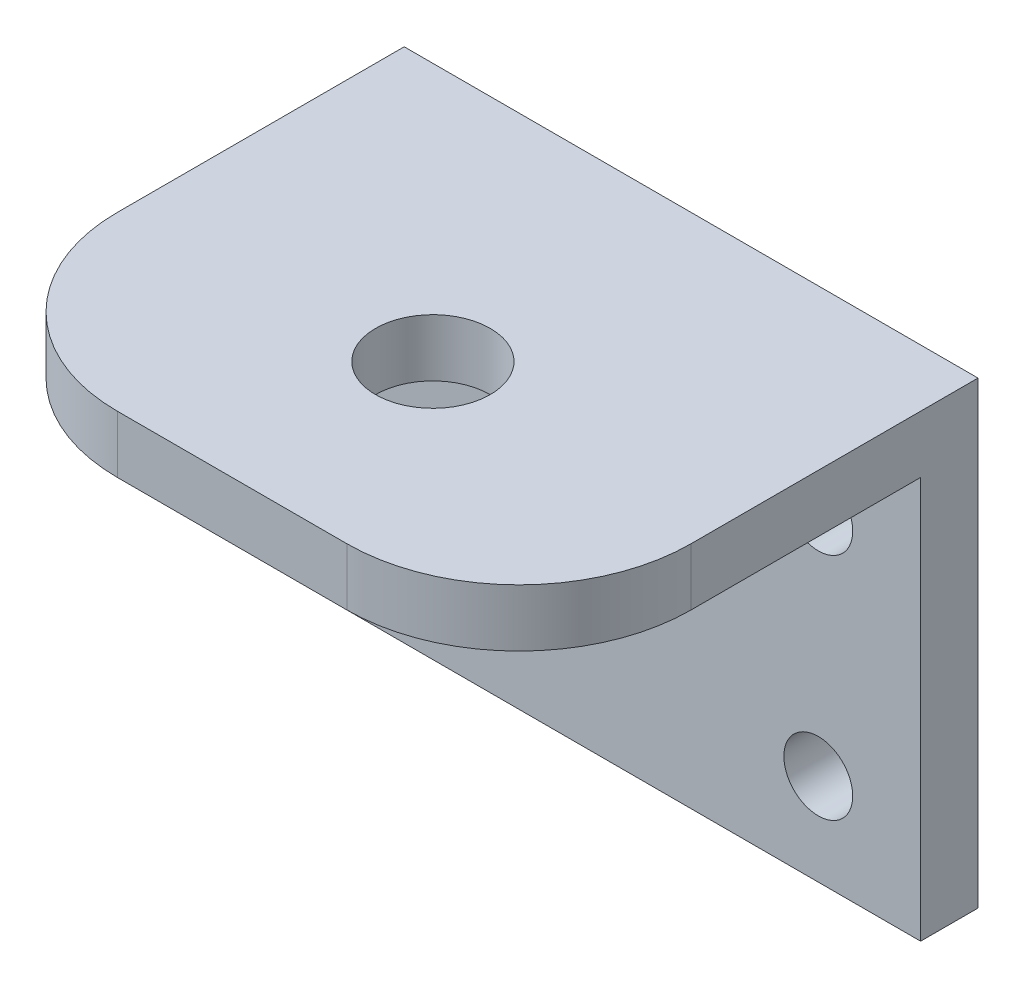
SolidWorks part; units mm, degrees
ref_plane "Front Plane" through (0, 0, 0) normal (0, 0, 1) x (1, 0, 0)
ref_plane "Top Plane" through (0, 0, 0) normal (0, 1, 0) x (1, 0, 0)
ref_plane "Right Plane" through (0, 0, 0) normal (1, 0, 0) x (0, 0, -1)
sketch "Sketch1" plane through (0, 0, 0) normal (0, 0, 1) x (1, 0, 0)
  line L1 (-25, -20) -> (25, -20)
  line L2 (-25, -20) -> (-25, 20)
  line L3 (-25, 20) -> (25, 20)
  line L4 (25, -20) -> (25, 20)
  line L5 (-25, -20) -> (25, 20) construction
  line L6 (-25, 20) -> (25, -20) construction
  point P0 (0, 0)
  dimension "D1" = 50
  dimension "D2" = 40
extrude "Boss-Extrude1" add sketch "Sketch1" along normal blind 40
sketch "Sketch2" plane through (0, 0, 0) normal (0, 0, -1) x (-1, 0, 0)
  line L1 (-16.0828, -12) -> (13.9172, -12) construction
  line L2 (-16.0828, -12) -> (-16.0828, 8) construction
  line L3 (-16.0828, 8) -> (13.9172, 8) construction
  line L4 (13.9172, -12) -> (13.9172, 8) construction
  line L5 (-16.0828, -12) -> (13.9172, 8) construction
  line L6 (-16.0828, 8) -> (13.9172, -12) construction
  line L7 (25, -20) -> (-25, -20) construction
  circle A0 centre (13.9172, -12) radius 3
  circle A1 centre (-16.0828, -12) radius 3
  circle A2 centre (-16.0828, 8) radius 3
  circle A3 centre (13.9172, 8) radius 3
  point P0 (-1.0828, -2)
  dimension "D3" = 6
  dimension "D1" = 30
  dimension "D2" = 20
  dimension "D4" = 18
sketch "Sketch5" plane through (0, -20, 0) normal (0, -1, 0) x (1, 0, 0)
  line L0 (25, 40) -> (-25, 0) construction
  line L1 (0, 0) -> (0, 40) construction
  line L2 (-25, 0) -> (25, 0) construction
  line L3 (-25, 40) -> (25, 40) construction
  line L4 (-25, 40) -> (-25, 0) construction
  line L5 (25, 40) -> (-25, 40)
  line L6 (25, 40) -> (25, 5)
  line L7 (25, 5) -> (-25, 5)
  line L8 (-25, 40) -> (-25, 5)
  dimension "D1" = 5
extrude "Cut-Extrude1" cut sketch "Sketch5" against normal blind 35
sketch "Sketch6" plane through (0, 15, 0) normal (0, -1, 0) x (1, 0, 0)
  line L0 (0, 40) -> (0, 5) construction
  line L2 (25, 40) -> (-25, 40) construction
  line L3 (-25, 5) -> (25, 5) construction
  circle A0 centre (0, 22.5) radius 5
  point P2 (0, 22.5)
  dimension "D1" = 10
extrude "Cut-Extrude2" cut sketch "Sketch6" against normal through all
extrude "Cut-Extrude3" cut sketch "Sketch2" against normal blind 10
fillet "Fillet1" radius 15 2 edges at (-25, 17.5, 40) (25, 17.5, 40)
